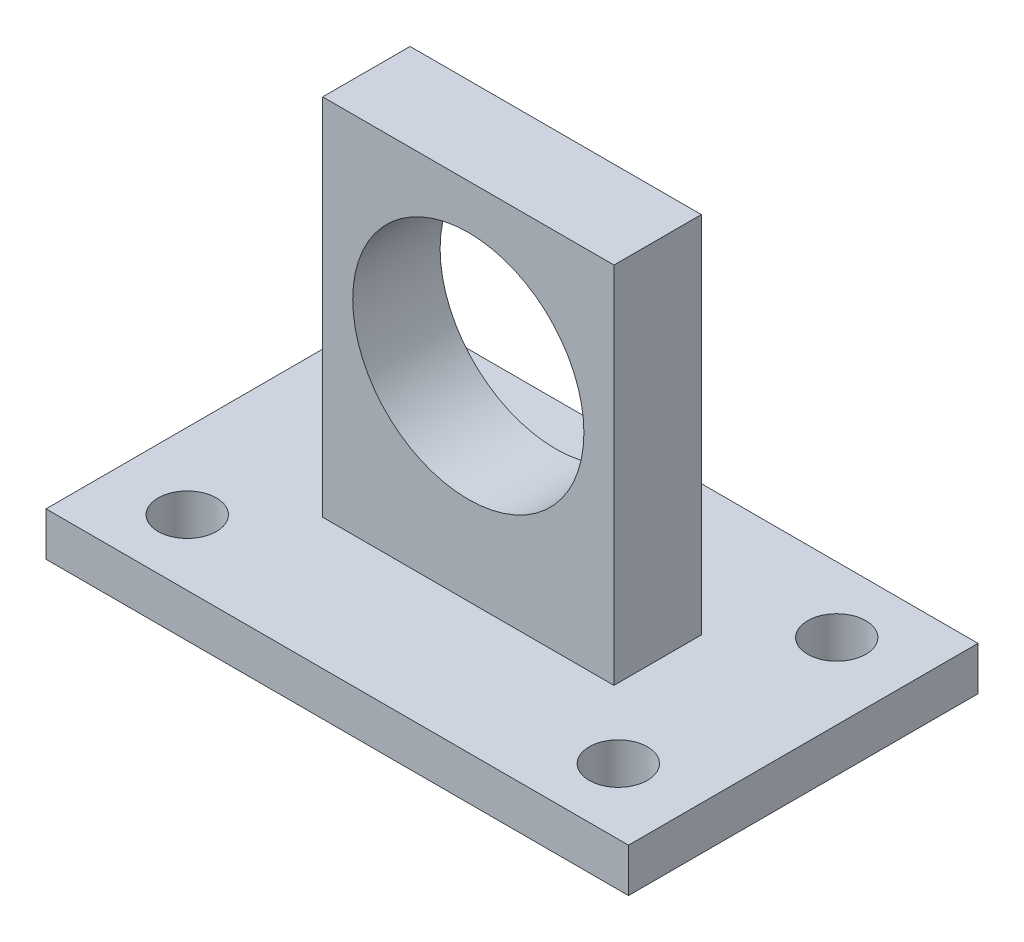
SolidWorks part; units mm, degrees
material "ABS"
ref_plane "Front" through (0, 0, 0) normal (0, 0, 1) x (1, 0, 0)
ref_plane "Top" through (0, 0, 0) normal (0, 1, 0) x (1, 0, 0)
ref_plane "Right" through (0, 0, 0) normal (1, 0, 0) x (0, 0, -1)
sketch "草图1" plane through (0, 0, 0) normal (0, 1, 0) x (1, 0, 0)
  line L0 (0, 0) -> (0, 12) construction
  line L1 (0, 0) -> (20, 0) construction
  line L2 (-20, 12) -> (20, 12)
  line L3 (20, 12) -> (20, -12)
  line L4 (-20, 12) -> (-20, -12)
  line L5 (-20, -12) -> (20, -12)
  line L6 (0, 0) -> (0, -7.5) construction
  line L7 (0, -7.5) -> (-14.8, -7.5) construction
  circle A0 centre (-14.8, -7.5) radius 2
  circle A1 centre (14.8, -7.5) radius 2
  circle A2 centre (-14.8, 7.5) radius 2
  circle A3 centre (14.8, 7.5) radius 2
  point P9 (-20, 0)
extrude "凸台-拉伸1" add sketch "草图1" along normal blind 3
sketch "草图2" plane through (0, 3, 0) normal (0, 1, 0) x (1, 0, 0)
  line L0 (0, 0) -> (0, 3) construction
  line L1 (0, 3) -> (20, 3) construction
  line L2 (20, -12) -> (20, 12) construction
  line L3 (20, 3) -> (20, -3) construction
  line L10 (0, 0) -> (0, -3) construction
  line L11 (0, -3) -> (-10, -3) construction
  line L12 (-10, -3) -> (-10, 3) construction
  line L14 (-10, 3) -> (-10, -3)
  line L15 (-10, -3) -> (10, -3)
  line L17 (-10, 3) -> (10, 3)
  line L18 (10, 3) -> (10, -3)
extrude "凸台-拉伸2" add sketch "草图2" along normal blind 25
sketch "草图3" plane through (0, 0, 3) normal (0, 0, 1) x (1, 0, 0)
  line L0 (0, 3) -> (0, 17) construction
  line L1 (-20, 3) -> (20, 3) construction
  circle A1 centre (0, 17) radius 7.9375
extrude "切除-拉伸1" cut sketch "草图3" against normal blind 10
